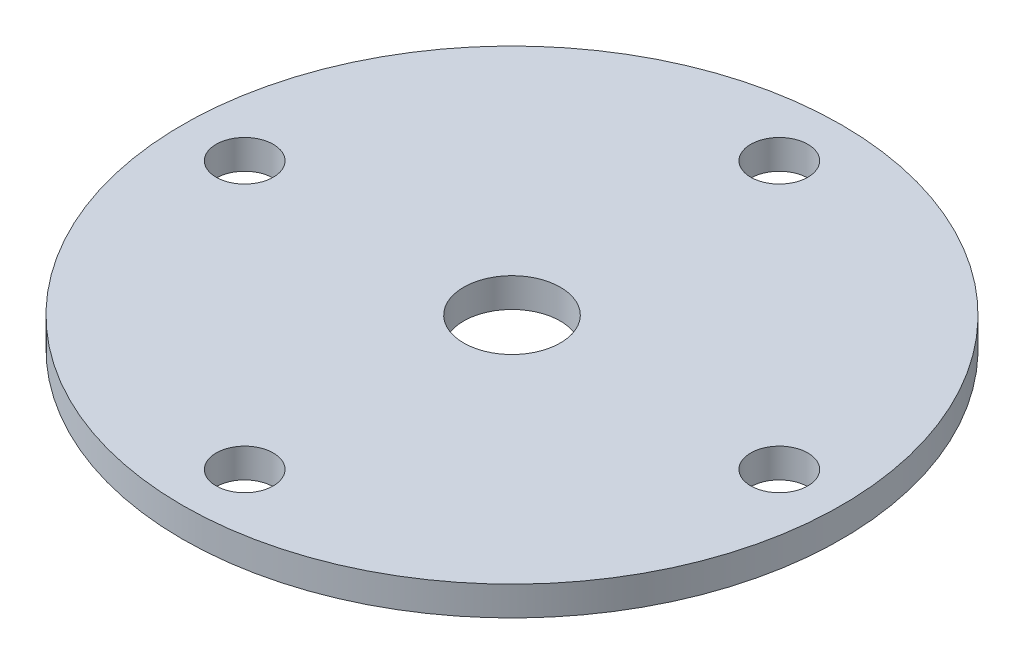
SolidWorks part; units mm, degrees
ref_plane "Front Plane" through (0, 0, 0) normal (0, 0, 1) x (1, 0, 0)
ref_plane "Top Plane" through (0, 0, 0) normal (0, 1, 0) x (1, 0, 0)
ref_plane "Right Plane" through (0, 0, 0) normal (1, 0, 0) x (0, 0, -1)
sketch "Sketch1" plane through (0, 0, 0) normal (0, 1, 0) x (1, 0, 0)
  line L0 (0, 24.45) -> (0, 4.95) construction
  circle A0 centre (0, 0) radius 4.95
  circle A1 centre (0, 0) radius 33.75
  circle A2 centre (0, 0) radius 27.375 construction
  circle A3 centre (0, 27.375) radius 2.925
  circle A4 centre (27.375, 0) radius 2.925
  circle A5 centre (0, -27.375) radius 2.925
  circle A6 centre (-27.375, 0) radius 2.925
  dimension "D1" = 9.9
  dimension "D3" = 5.85
  dimension "D4" = 67.5
  dimension "D2" = 19.5
extrude "Boss-Extrude1" add sketch "Sketch1" along normal blind 3
